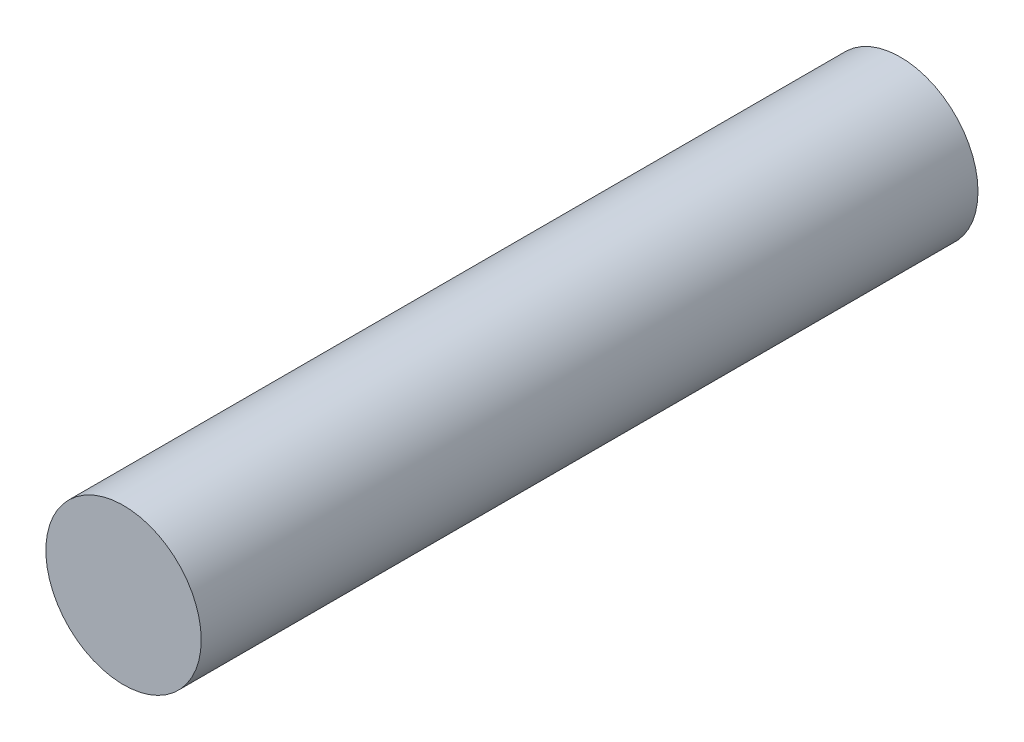
SolidWorks part; units mm, degrees
ref_plane "Front Plane" through (0, 0, 0) normal (0, 0, 1) x (1, 0, 0)
ref_plane "Top Plane" through (0, 0, 0) normal (0, 1, 0) x (1, 0, 0)
ref_plane "Right Plane" through (0, 0, 0) normal (1, 0, 0) x (0, 0, -1)
sketch "Sketch1" plane through (0, 0, 0) normal (0, 0, 1) x (1, 0, 0)
  circle A0 centre (0, 0) radius 1.5
  dimension "D1" = 3
extrude "Boss-Extrude1" add sketch "Sketch1" along normal blind 15 contours A0
